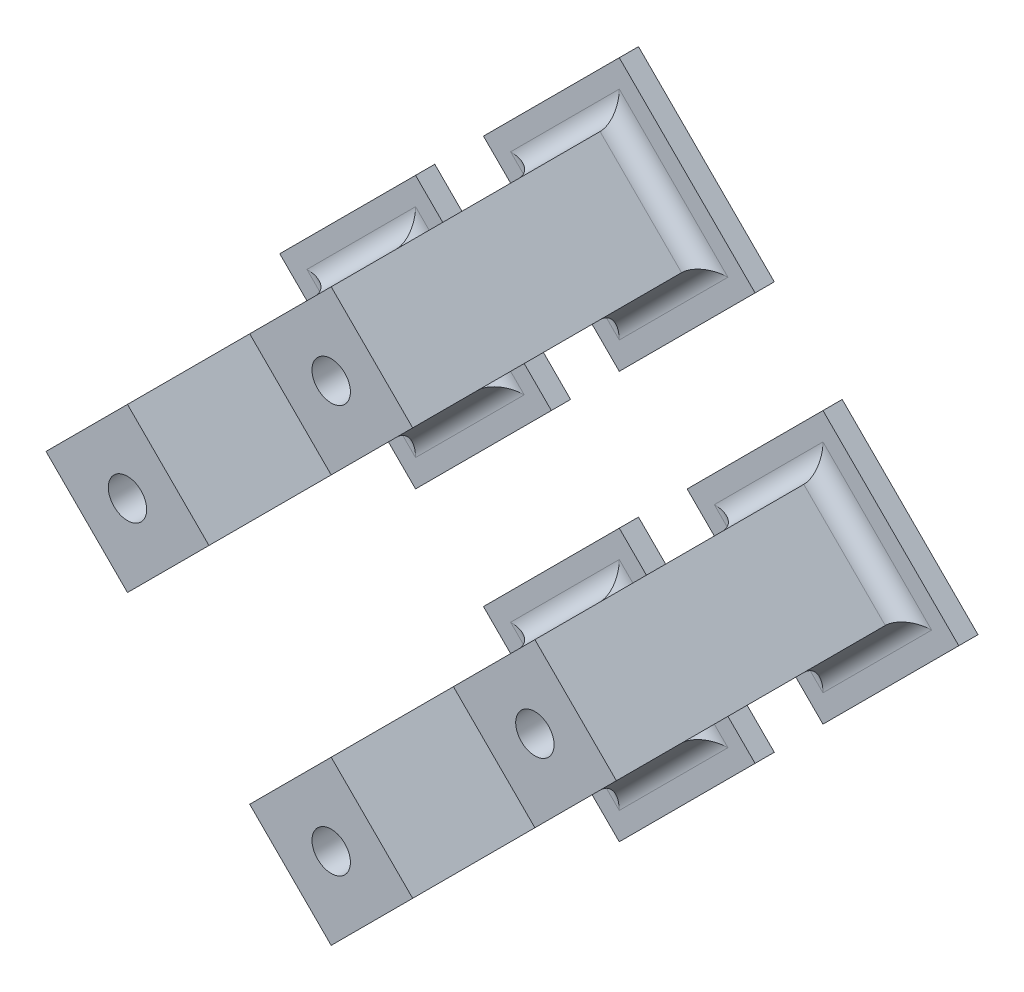
SolidWorks part; units mm, degrees
ref_plane "Front Plane" through (0, 0, 0) normal (0, 0, 1) x (1, 0, 0)
ref_plane "Top Plane" through (0, 0, 0) normal (0, 1, 0) x (1, 0, 0)
ref_plane "Right Plane" through (0, 0, 0) normal (1, 0, 0) x (0, 0, -1)
sketch "Sketch1" plane through (0, 0, 0) normal (0, 0, 1) x (1, 0, 0)
  line L0 (-7.0711, 0) -> (0, 7.0711)
  line L1 (-7.0711, 0) -> (0, -7.0711)
  line L2 (0, 7.0711) -> (7.0711, 0)
  line L3 (0, -7.0711) -> (7.0711, 0)
  line L4 (-7.0711, 0) -> (7.0711, 0) construction
  line L5 (0, 7.0711) -> (0, -7.0711) construction
  point P1 (0, 0)
  dimension "D1" = 10
extrude "Base" add sketch "Sketch1" along normal blind 1
sketch "Sketch2" plane through (0, 0, 1) normal (0, 0, 1) x (1, 0, 0)
  line L0 (0, -4.2426) -> (4.2426, 0)
  line L1 (0, -4.2426) -> (-4.2426, 0)
  line L2 (4.2426, 0) -> (0, 4.2426)
  line L3 (-4.2426, 0) -> (0, 4.2426)
  line L4 (0, -4.2426) -> (0, 4.2426) construction
  line L5 (4.2426, 0) -> (-4.2426, 0) construction
  point P1 (0, 0)
  dimension "D1" = 6
extrude "Boss-Extrude2" add sketch "Sketch2" along normal blind 15
sketch "Sketch3" plane through (0, 0, 16) normal (0, 0, 1) x (1, 0, 0)
  circle A0 centre (0, 0) radius 1
  dimension "D1" = 2
extrude "Cut-Extrude1" cut sketch "Sketch3" against normal through all
fillet "Fillet1" radius 1 4 edges at (2.1213, 2.1213, 1) (2.1213, -2.1213, 1) (-2.1213, -2.1213, 1) (-2.1213, 2.1213, 1)
sketch "Sketch4" plane through (0, 0, 0) normal (0, 0, -1) x (-1, 0, 0)
  circle A0 centre (0, 0) radius 3
  dimension "D1" = 6
extrude "Cut-Extrude2" cut sketch "Sketch4" against normal blind 1
pattern_linear "LPattern1" count 2 spacing 15 along (-0.7071, 0.7071, 0) count 2 spacing 15 along (-0.7071, -0.7071, 0) of "Boss-Extrude2"
